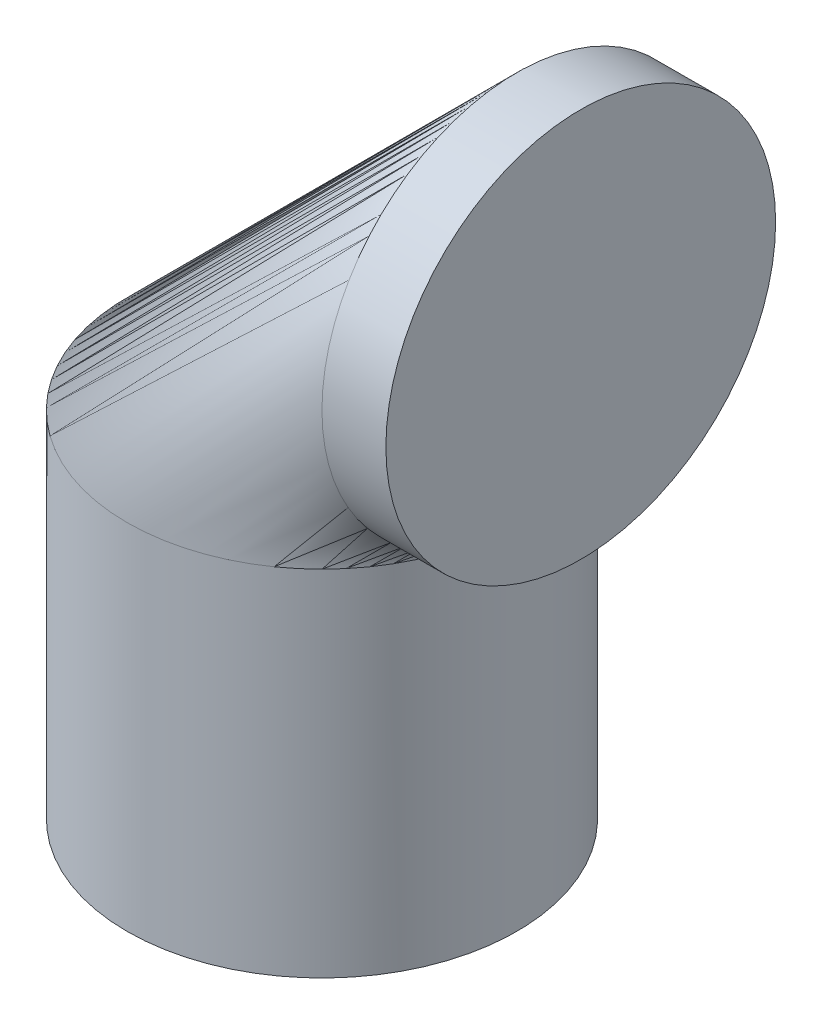
SolidWorks part; units mm, degrees
ref_plane "Front Plane" through (0, 0, 0) normal (0, 0, 1) x (1, 0, 0)
ref_plane "Top Plane" through (0, 0, 0) normal (0, 1, 0) x (1, 0, 0)
ref_plane "Right Plane" through (0, 0, 0) normal (1, 0, 0) x (0, 0, -1)
sketch "Sketch4" plane through (0, 0, 0) normal (0, 0, 1) x (1, 0, 0)
  line L0 (0, 0) -> (0, 45.42)
  line L1 (25, 70.42) -> (33.2, 70.42)
  arc A0 (0, 45.42) -> (25, 70.42) centre (25, 45.42) cw
  point P7 (0, 70.42)
  dimension "D3" = 25
  dimension "D1" = 70.42
  dimension "D2" = 33.2
sketch "Sketch5" plane through (0, 0, 0) normal (0, 1, 0) x (1, 0, 0)
  circle A0 centre (0, 0) radius 25
  dimension "D1" = 50
sweep "Sweep2" add profiles "Sketch5" path "Sketch4"
